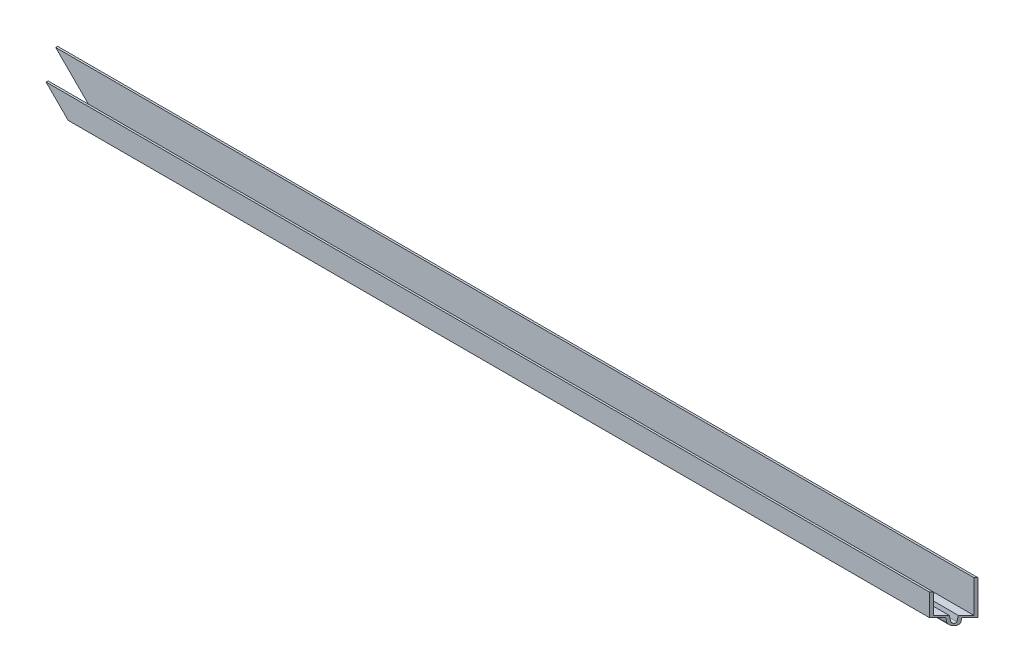
SolidWorks part; units mm, degrees
material "6063-O"
ref_plane "Front Plane" through (0, 0, 0) normal (0, 0, 1) x (1, 0, 0)
ref_plane "Top Plane" through (0, 0, 0) normal (0, 1, 0) x (1, 0, 0)
ref_plane "Right Plane" through (0, 0, 0) normal (1, 0, 0) x (0, 0, -1)
other "Configuration Table"
sketch "Sketch1" plane through (0, 0, 0) normal (1, 0, 0) x (0, 0, -1)
  line L0 (7.62, 0) -> (7.62, -21.844)
  line L1 (7.62, -21.844) -> (2.54, -21.844)
  line L2 (-2.54, -21.844) -> (-2.2022, -24.2477)
  line L3 (2.2022, -24.2477) -> (2.54, -21.844)
  line L4 (-2.54, -21.844) -> (-7.62, -21.844)
  line L5 (-7.62, -21.844) -> (-7.62, -7.874)
  line L6 (6.35, 0) -> (6.35, -20.574)
  line L7 (6.35, -20.574) -> (1.436, -20.574)
  line L8 (0.9445, -24.0709) -> (1.436, -20.574)
  line L9 (-1.436, -20.574) -> (-0.9445, -24.0709)
  line L10 (-1.436, -20.574) -> (-6.35, -20.574)
  line L11 (-6.35, -20.574) -> (-6.35, -7.874)
  line L12 (7.62, 0) -> (6.35, 0)
  line L13 (-7.62, -7.874) -> (-6.35, -7.874)
  line L14 (0, 0) -> (0, -30.4009) construction
  arc A0 (-2.2022, -24.2477) -> (2.2022, -24.2477) centre (0, -23.9382) ccw
  arc A1 (-0.9445, -24.0709) -> (0.9445, -24.0709) centre (0, -23.9382) ccw
  dimension "D1" = 15.24
  dimension "D2" = 4.318
  dimension "D3" = 21.844
  dimension "D4" = 13.97
  dimension "D5" = 12.7
  dimension "D6" = 82
  dimension "D7" = 5.08
extrude "Boss-Extrude1" add sketch "Sketch1" along normal mid plane 579.4375
sketch "Sketch4" plane through (0, 0, 0) normal (0, 1, 0) x (1, 0, 0)
  line L0 (-289.7187, 7.62) -> (-274.4787, -7.62)
  line L1 (289.7187, -7.62) -> (-289.7187, -7.62) construction
  line L2 (-274.4787, -7.62) -> (-289.7187, -7.62)
  line L3 (-289.7187, -7.62) -> (-289.7187, 7.62)
extrude "Cut-Top-Left-Front" [suppressed] cut sketch "Sketch4" against normal through all
sketch "Sketch9" plane through (0, 0, 7.62) normal (0, 0, 1) x (1, 0, 0)
  line L0 (-289.7187, -26.162) -> (-263.5567, 0)
  line L1 (289.7187, 0) -> (-289.7187, 0) construction
  line L2 (-263.5567, 0) -> (-289.7187, 0)
  line L3 (-289.7187, 0) -> (-289.7187, -26.162)
extrude "Cut-Front-Left-Top" [suppressed] cut sketch "Sketch9" against normal through all
sketch "Sketch11" plane through (0, 0, 7.62) normal (0, 0, 1) x (1, 0, 0)
  line L0 (289.7187, 0) -> (263.5567, -26.162)
  line L1 (-289.7187, -26.162) -> (289.7187, -26.162) construction
  line L2 (263.5567, -26.162) -> (289.7187, -26.162)
  line L3 (289.7187, -26.162) -> (289.7187, 0)
extrude "Cut-Front-Right-Bottom" [suppressed] cut sketch "Sketch11" against normal through all
sketch "Sketch7" plane through (0, 0, 7.62) normal (0, 0, 1) x (1, 0, 0)
  line L0 (289.7187, -26.162) -> (263.5567, 0)
  line L2 (263.5567, 0) -> (289.7187, 0)
  line L4 (289.7187, 0) -> (289.7187, -26.162)
  line L5 (289.7187, -7.874) -> (289.7187, -21.844) construction
  line L6 (289.7187, 0) -> (-289.7187, 0) construction
extrude "Cut-Front-Right-Top" [suppressed] cut sketch "Sketch7" against normal through all
sketch "Sketch2" plane through (0, 0, 0) normal (0, 1, 0) x (1, 0, 0)
  line L0 (289.7187, 7.62) -> (274.4787, -7.62)
  line L1 (289.7187, -7.62) -> (-289.7187, -7.62) construction
  line L2 (274.4787, -7.62) -> (289.7187, -7.62)
  line L3 (289.7187, -7.62) -> (289.7187, 7.62)
extrude "Cut-Top-Right-Front" cut sketch "Sketch2" against normal through all
sketch "Sketch12" plane through (0, 0, 7.62) normal (0, 0, 1) x (1, 0, 0)
  line L0 (-289.7187, 0) -> (-263.5567, -26.162)
  line L1 (-289.7187, -26.162) -> (282.0987, -26.162) construction
  line L2 (-263.5567, -26.162) -> (-289.7187, -26.162)
  line L3 (-289.7187, -26.162) -> (-289.7187, 0)
extrude "Cut-Front-Left-Bottom" cut sketch "Sketch12" against normal through all
